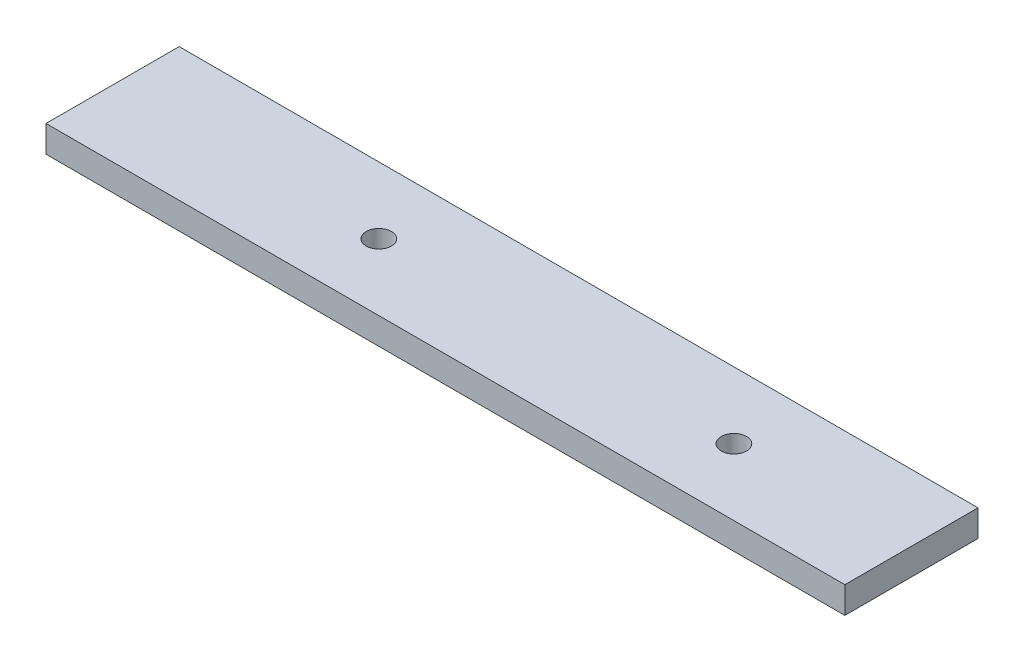
SolidWorks part; units mm, degrees
ref_plane "Front Plane" through (0, 0, 0) normal (0, 0, 1) x (1, 0, 0)
ref_plane "Top Plane" through (0, 0, 0) normal (0, 1, 0) x (1, 0, 0)
ref_plane "Right Plane" through (0, 0, 0) normal (1, 0, 0) x (0, 0, -1)
sketch "Sketch1" plane through (0, 0, 0) normal (0, 1, 0) x (1, 0, 0)
  line L1 (-50, -7.5) -> (50, -7.5)
  line L2 (-50, -7.5) -> (-50, 7.5)
  line L3 (-50, 7.5) -> (50, 7.5)
  line L4 (50, -7.5) -> (50, 7.5)
  line L5 (-50, -7.5) -> (50, 7.5) construction
  line L6 (-50, 7.5) -> (50, -7.5) construction
  point P0 (0, 0)
  dimension "D1" = 100
  dimension "D2" = 15
extrude "Boss-Extrude1" add sketch "Sketch1" along normal blind 3
sketch "Sketch2" plane through (0, 3, 0) normal (0, 1, 0) x (1, 0, 0)
  line L0 (82.403, 0) -> (-71.2013, 0) construction
  line L1 (-50, 7.5) -> (-50, -7.5) construction
  circle A0 centre (-28.87, 0) radius 1
  circle A1 centre (-42, 0) radius 1
  dimension "D1" = 2
  dimension "D2" = 13.13
  dimension "D3" = 8
extrude "Cut-Extrude1" cut sketch "Sketch2" against normal blind 10
sketch "Sketch3" plane through (0, 0, 0) normal (0, -1, 0) x (1, 0, 0)
  circle A0 centre (-35.4341, -0.0065) radius 2.5
  dimension "D1" = 5
extrude "Cut-Extrude2" cut sketch "Sketch3" against normal blind 10
sketch "Sketch4" plane through (0, 0, 0) normal (0, -1, 0) x (-1, 0, 0)
  line L0 (50, 1.885) -> (50, 7.5)
  line L1 (50, 7.5) -> (50, -7.5) construction
  line L2 (41.7628, 3.5776) -> (39.063, 7.5)
  line L3 (43.6768, 2.4208) -> (50, 1.885)
  line L4 (37.5744, 2.9254) -> (49.7791, 1.9162) construction
  line L5 (61.6671, 0) -> (-13.1622, 0) construction
  line L7 (13.7733, -21.913) -> (15.2746, -21.913) construction
  line L9 (-50, 7.5) -> (50, 7.5) construction
  line L10 (50, 7.5) -> (39.063, 7.5)
  arc A0 (49.7752, -1.9317) -> (49.7791, 1.9162) centre (49.62, -0.0076) ccw construction
  arc A1 (43.6768, 2.4208) -> (41.7628, 3.5776) centre (44, 5.1175) cw
  dimension "D3" = 2.716
  dimension "D2" = 6
  dimension "D4" = 4.7617
  dimension "D5" = 55.46
extrude "Cut-Extrude3" cut sketch "Sketch4" against normal blind 10
mirror "Mirror1" about plane through (0, 0, 0) normal (0, 0, 1) of "Cut-Extrude3"
fillet "Fillet1" radius 5 2 edges at (-39.063, 1.5, 7.5) (-39.063, 1.5, -7.5)
fillet "Fillet2" radius 1 2 edges at (-50, 1.5, 1.885) (-50, 1.5, -1.885)
sketch "Sketch5" plane through (0, 0, 0) normal (0, -1, 0) x (1, 0, 0)
  line L0 (0, 0) -> (59.3331, 0) construction
  line L1 (50, 7.5) -> (50, -7.5) construction
  circle A0 centre (17.75, 0) radius 1
  circle A1 centre (45, 0) radius 1
  dimension "D1" = 2
  dimension "D2" = 27.25
  dimension "D3" = 5
extrude "Cut-Extrude4" [suppressed] cut sketch "Sketch5" against normal blind 10
sketch "Sketch6" plane through (0, 3, 0) normal (0, 1, 0) x (1, 0, 0)
  line L0 (0, 0) -> (56.0032, 0) construction
  line L1 (50, -7.5) -> (50, 7.5) construction
  line L2 (43.5, 6.5) -> (19.75, 6.5)
  line L3 (43.5, 6.5) -> (43.5, -6.5)
  line L4 (43.5, -6.5) -> (19.75, -6.5)
  line L5 (19.75, 6.5) -> (19.75, -6.5)
  line L6 (43.5, 6.5) -> (19.75, -6.5) construction
  line L7 (43.5, -6.5) -> (19.75, 6.5) construction
  line L8 (-36.4345, -7.5) -> (50, -7.5) construction
  point P3 (31.625, 0)
  dimension "D1" = 6.5
  dimension "D2" = 23.75
  dimension "D3" = 1
extrude "Cut-Extrude5" [suppressed] cut sketch "Sketch6" against normal blind 10
sketch "Sketch7" plane through (50, 0, 0) normal (1, 0, 0) x (0, 0, -1)
  line L1 (-7.5, 3) -> (7.5, 3)
  line L2 (-7.5, 3) -> (-7.5, 0)
  line L3 (-7.5, 0) -> (7.5, 0)
  line L4 (7.5, 3) -> (7.5, 0)
extrude "Boss-Extrude2" add sketch "Sketch7" along normal blind 20
sketch "Sketch8" plane through (0, 3, 0) normal (0, 1, 0) x (1, 0, 0)
  line L0 (-20, 7.5) -> (-20, -7.5)
  line L1 (70, 7.5) -> (-36.4345, 7.5) construction
  line L2 (-36.4345, -7.5) -> (70, -7.5) construction
  line L3 (-20, -7.5) -> (-61.1165, -7.5)
  line L4 (-61.1165, -7.5) -> (-61.1165, 7.5)
  line L5 (-61.1165, 7.5) -> (-20, 7.5)
  line L6 (70, 7.5) -> (70, -7.5) construction
  dimension "D1" = 41.1165
  dimension "D2" = 90
extrude "Cut-Extrude6" cut sketch "Sketch8" against normal blind 20
sketch "Sketch9" plane through (0, 3, 0) normal (0, 1, 0) x (1, 0, 0)
  line L0 (-36.2305, 0) -> (82.225, 0) construction
  line L1 (70, 7.5) -> (70, -7.5) construction
  circle A0 centre (50, 0) radius 1.425
  circle A1 centre (10, 0) radius 1.425
  dimension "D1" = 2.85
  dimension "D2" = 40
  dimension "D3" = 20
extrude "Cut-Extrude7" cut sketch "Sketch9" against normal blind 20
